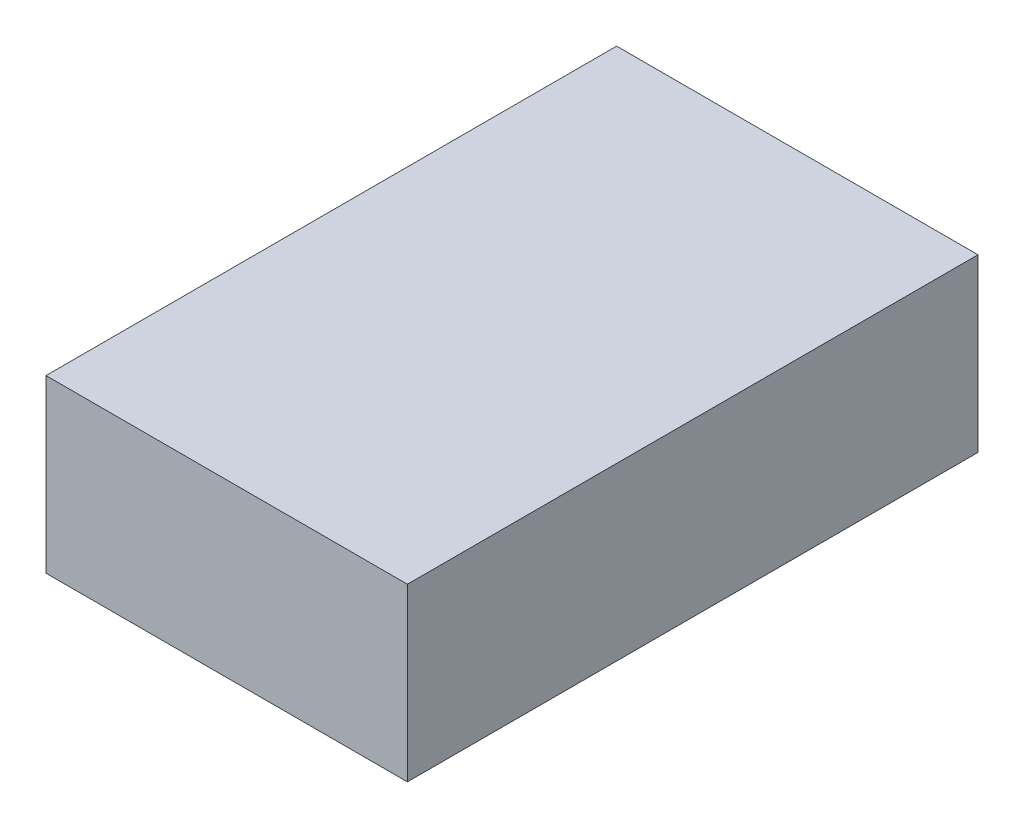
SolidWorks part; units mm, degrees
ref_plane "Front" through (0, 0, 0) normal (0, 0, 1) x (1, 0, 0)
ref_plane "Top" through (0, 0, 0) normal (0, 1, 0) x (1, 0, 0)
ref_plane "Right" through (0, 0, 0) normal (1, 0, 0) x (0, 0, -1)
sketch "Sketch1" plane through (0, 0, 0) normal (0, 1, 0) x (1, 0, 0)
  line L1 (0, 0) -> (19, 0)
  line L2 (0, 0) -> (0, 30)
  line L3 (0, 30) -> (19, 30)
  line L4 (19, 0) -> (19, 30)
  dimension "D1" = 30
  dimension "D2" = 19
extrude "Boss-Extrude1" add sketch "Sketch1" along normal blind 9
